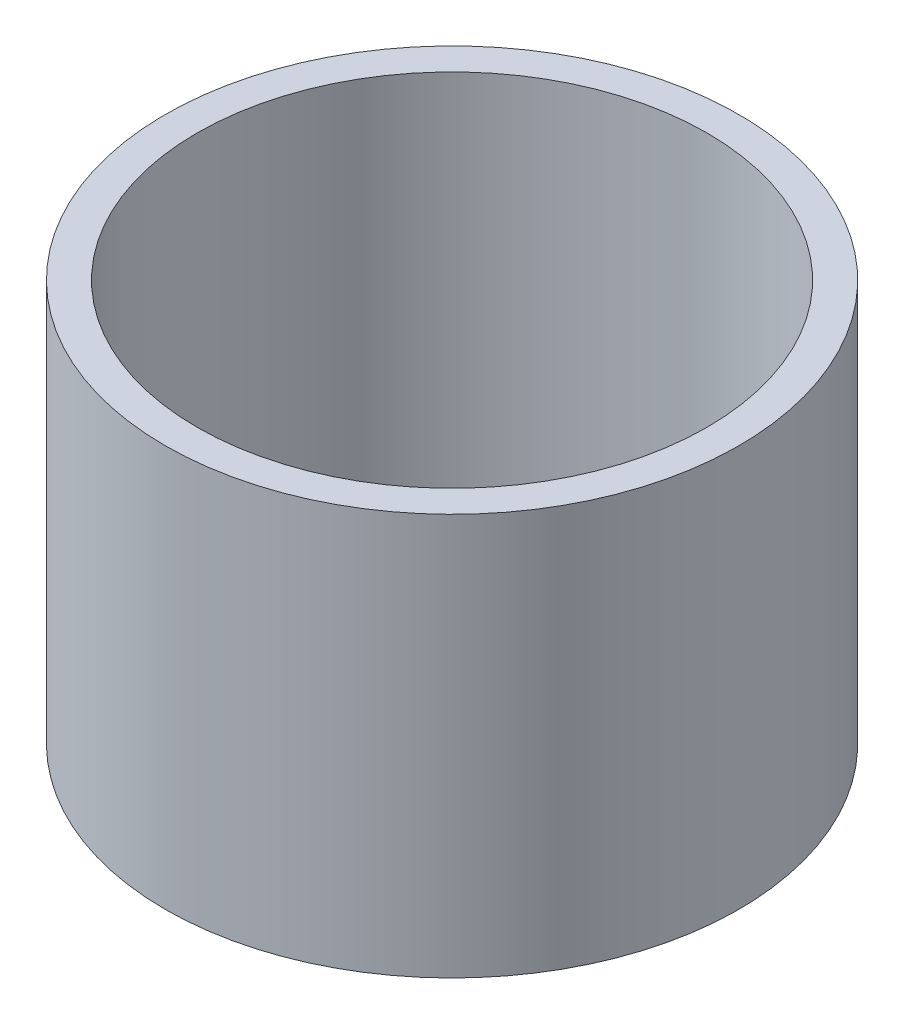
SolidWorks part; units mm, degrees
ref_plane "Front Plane" through (0, 0, 0) normal (0, 0, 1) x (1, 0, 0)
ref_plane "Top Plane" through (0, 0, 0) normal (0, 1, 0) x (1, 0, 0)
ref_plane "Right Plane" through (0, 0, 0) normal (1, 0, 0) x (0, 0, -1)
sketch "Sketch1" plane through (0, 0, 0) normal (0, 1, 0) x (1, 0, 0)
  circle A0 centre (0, 0) radius 9
  circle A1 centre (0, 0) radius 8
extrude "Boss-Extrude1" add sketch "Sketch1" along normal blind 12.6
